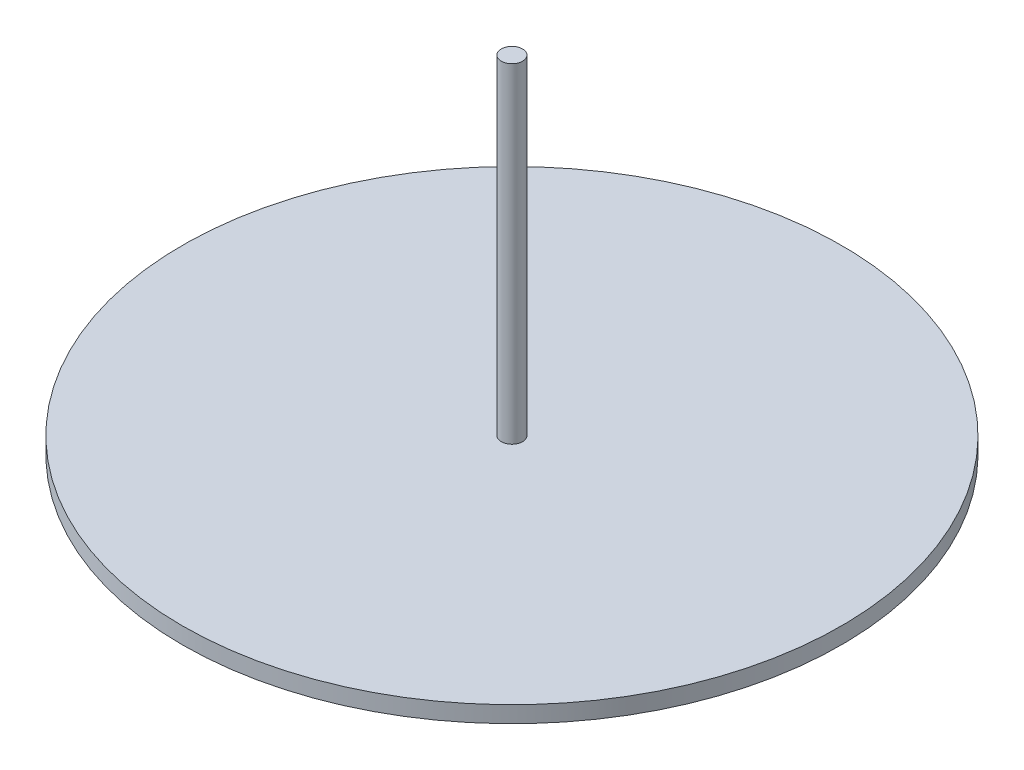
SolidWorks part; units mm, degrees
ref_plane "Front Plane" through (0, 0, 0) normal (0, 0, 1) x (1, 0, 0)
ref_plane "Top Plane" through (0, 0, 0) normal (0, 1, 0) x (1, 0, 0)
ref_plane "Right Plane" through (0, 0, 0) normal (1, 0, 0) x (0, 0, -1)
sketch "Sketch3" plane through (0, 0, 0) normal (0, 1, 0) x (1, 0, 0)
  circle A0 centre (0, 0) radius 100
  dimension "D1" = 200
extrude "Boss-Extrude2" add sketch "Sketch3" along normal blind 5
sketch "Sketch4" plane through (0, 5, 0) normal (0, 1, 0) x (1, 0, 0)
  circle A0 centre (0, 0) radius 3.225
  dimension "D1" = 6.45
extrude "Boss-Extrude3" add sketch "Sketch4" along normal blind 100
